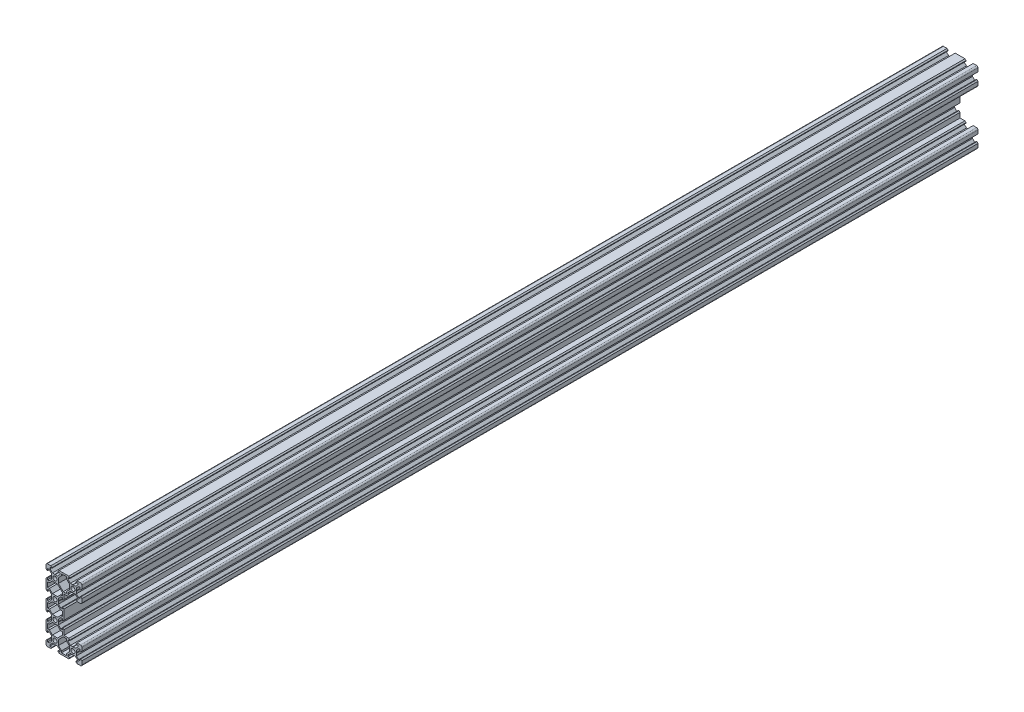
SolidWorks part; units mm, degrees
material "6061-T6 (SS)"
ref_plane "Front Plane" through (0, 0, 0) normal (0, 0, 1) x (1, 0, 0)
ref_plane "Top Plane" through (0, 0, 0) normal (0, 1, 0) x (1, 0, 0)
ref_plane "Right Plane" through (0, 0, 0) normal (1, 0, 0) x (0, 0, -1)
sketch "Sketch1" plane through (0, 0, 0) normal (0, 0, 1) x (1, 0, 0)
  line L0 (-20, -38.5) -> (-20, 38.5)
  line L1 (-18.5, 40) -> (18.5, 40)
  line L2 (20, 38.5) -> (20, 21.5)
  line L3 (18.5, 20) -> (0, 20)
  line L4 (0, 20) -> (0, -20)
  line L5 (0, 0) -> (-20, 0) construction
  line L6 (18.5, -20) -> (0, -20)
  line L7 (20, -38.5) -> (20, -21.5)
  line L8 (-18.5, -40) -> (18.5, -40)
  line L9 (20, 30) -> (10, 30) construction
  line L10 (-10, 0) -> (-10, 10) construction
  arc A0 (-18.5, -40) -> (-20, -38.5) centre (-18.5, -38.5) cw
  arc A1 (20, -38.5) -> (18.5, -40) centre (18.5, -38.5) cw
  arc A2 (18.5, -20) -> (20, -21.5) centre (18.5, -21.5) cw
  arc A3 (20, 21.5) -> (18.5, 20) centre (18.5, 21.5) cw
  arc A4 (18.5, 40) -> (20, 38.5) centre (18.5, 38.5) cw
  arc A5 (-20, 38.5) -> (-18.5, 40) centre (-18.5, 38.5) cw
  circle A6 centre (10, 30) radius 2.3
  circle A7 centre (-10, 30) radius 2.3
  circle A8 centre (-10, 10) radius 2.3
  circle A9 centre (-10, -10) radius 2.3
  circle A10 centre (10, -30) radius 2.3
  circle A11 centre (-10, -30) radius 2.3
  point P13 (-20, -40)
  point P16 (20, -40)
  point P19 (20, -20)
  point P22 (20, 20)
  point P25 (20, 40)
  point P28 (-20, 40)
  line B0 (-10, 30) -> (-10, 40) construction
  line B1 (-10, 33.69) -> (-10.21, 33.9)
  line B2 (-10.21, 33.9) -> (-12.8393, 33.9)
  line B3 (-12.8393, 33.9) -> (-15.5, 36.5607)
  line B4 (-15.5, 36.5607) -> (-15.5, 38.2)
  line B5 (-15.5, 38.2) -> (-13.395, 38.2)
  line B6 (-13.395, 38.2) -> (-13.395, 38.815)
  line B7 (-13.395, 38.815) -> (-14.58, 40)
  line B8 (-14.58, 40) -> (-5.42, 40)
  line B9 (-10, 30) -> (-15.9132, 35.9132) construction
  line B10 (-6.605, 38.815) -> (-5.42, 40)
  line B11 (-6.605, 38.2) -> (-6.605, 38.815)
  line B12 (-4.5, 38.2) -> (-6.605, 38.2)
  line B13 (-4.5, 36.5607) -> (-4.5, 38.2)
  line B14 (-7.1607, 33.9) -> (-4.5, 36.5607)
  line B15 (-9.79, 33.9) -> (-7.1607, 33.9)
  line B16 (-10, 33.69) -> (-9.79, 33.9)
  line B17 (10, 30) -> (10, 40) construction
  line B18 (10, 33.69) -> (9.79, 33.9)
  line B19 (9.79, 33.9) -> (7.1607, 33.9)
  line B20 (7.1607, 33.9) -> (4.5, 36.5607)
  line B21 (4.5, 36.5607) -> (4.5, 38.2)
  line B22 (4.5, 38.2) -> (6.605, 38.2)
  line B23 (6.605, 38.2) -> (6.605, 38.815)
  line B24 (6.605, 38.815) -> (5.42, 40)
  line B25 (5.42, 40) -> (14.58, 40)
  line B26 (10, 30) -> (4.0868, 35.9132) construction
  line B27 (13.395, 38.815) -> (14.58, 40)
  line B28 (13.395, 38.2) -> (13.395, 38.815)
  line B29 (15.5, 38.2) -> (13.395, 38.2)
  line B30 (15.5, 36.5607) -> (15.5, 38.2)
  line B31 (12.8393, 33.9) -> (15.5, 36.5607)
  line B32 (10.21, 33.9) -> (12.8393, 33.9)
  line B33 (10, 33.69) -> (10.21, 33.9)
  line B34 (10, -30) -> (10, -20) construction
  line B35 (10, -26.31) -> (9.79, -26.1)
  line B36 (9.79, -26.1) -> (7.1607, -26.1)
  line B37 (7.1607, -26.1) -> (4.5, -23.4393)
  line B38 (4.5, -23.4393) -> (4.5, -21.8)
  line B39 (4.5, -21.8) -> (6.605, -21.8)
  line B40 (6.605, -21.8) -> (6.605, -21.185)
  line B41 (6.605, -21.185) -> (5.42, -20)
  line B42 (5.42, -20) -> (14.58, -20)
  line B43 (10, -30) -> (4.0868, -24.0868) construction
  line B44 (13.395, -21.185) -> (14.58, -20)
  line B45 (13.395, -21.8) -> (13.395, -21.185)
  line B46 (15.5, -21.8) -> (13.395, -21.8)
  line B47 (15.5, -23.4393) -> (15.5, -21.8)
  line B48 (12.8393, -26.1) -> (15.5, -23.4393)
  line B49 (10.21, -26.1) -> (12.8393, -26.1)
  line B50 (10, -26.31) -> (10.21, -26.1)
  line B51 (-10, 30) -> (-20, 30) construction
  line B52 (-13.69, 30) -> (-13.9, 29.79)
  line B53 (-13.9, 29.79) -> (-13.9, 27.1607)
  line B54 (-13.9, 27.1607) -> (-16.5607, 24.5)
  line B55 (-16.5607, 24.5) -> (-18.2, 24.5)
  line B56 (-18.2, 24.5) -> (-18.2, 26.605)
  line B57 (-18.2, 26.605) -> (-18.815, 26.605)
  line B58 (-18.815, 26.605) -> (-20, 25.42)
  line B59 (-20, 25.42) -> (-20, 34.58)
  line B60 (-10, 30) -> (-15.9132, 24.0868) construction
  line B61 (-18.815, 33.395) -> (-20, 34.58)
  line B62 (-18.2, 33.395) -> (-18.815, 33.395)
  line B63 (-18.2, 35.5) -> (-18.2, 33.395)
  line B64 (-16.5607, 35.5) -> (-18.2, 35.5)
  line B65 (-13.9, 32.8393) -> (-16.5607, 35.5)
  line B66 (-13.9, 30.21) -> (-13.9, 32.8393)
  line B67 (-13.69, 30) -> (-13.9, 30.21)
  line B68 (-10, 10) -> (-20, 10) construction
  line B69 (-13.69, 10) -> (-13.9, 9.79)
  line B70 (-13.9, 9.79) -> (-13.9, 7.1607)
  line B71 (-13.9, 7.1607) -> (-16.5607, 4.5)
  line B72 (-16.5607, 4.5) -> (-18.2, 4.5)
  line B73 (-18.2, 4.5) -> (-18.2, 6.605)
  line B74 (-18.2, 6.605) -> (-18.815, 6.605)
  line B75 (-18.815, 6.605) -> (-20, 5.42)
  line B76 (-20, 5.42) -> (-20, 14.58)
  line B77 (-10, 10) -> (-15.9132, 4.0868) construction
  line B78 (-18.815, 13.395) -> (-20, 14.58)
  line B79 (-18.2, 13.395) -> (-18.815, 13.395)
  line B80 (-18.2, 15.5) -> (-18.2, 13.395)
  line B81 (-16.5607, 15.5) -> (-18.2, 15.5)
  line B82 (-13.9, 12.8393) -> (-16.5607, 15.5)
  line B83 (-13.9, 10.21) -> (-13.9, 12.8393)
  line B84 (-13.69, 10) -> (-13.9, 10.21)
  line B85 (-10, -10) -> (-20, -10) construction
  line B86 (-13.69, -10) -> (-13.9, -10.21)
  line B87 (-13.9, -10.21) -> (-13.9, -12.8393)
  line B88 (-13.9, -12.8393) -> (-16.5607, -15.5)
  line B89 (-16.5607, -15.5) -> (-18.2, -15.5)
  line B90 (-18.2, -15.5) -> (-18.2, -13.395)
  line B91 (-18.2, -13.395) -> (-18.815, -13.395)
  line B92 (-18.815, -13.395) -> (-20, -14.58)
  line B93 (-20, -14.58) -> (-20, -5.42)
  line B94 (-10, -10) -> (-15.9132, -15.9132) construction
  line B95 (-18.815, -6.605) -> (-20, -5.42)
  line B96 (-18.2, -6.605) -> (-18.815, -6.605)
  line B97 (-18.2, -4.5) -> (-18.2, -6.605)
  line B98 (-16.5607, -4.5) -> (-18.2, -4.5)
  line B99 (-13.9, -7.1607) -> (-16.5607, -4.5)
  line B100 (-13.9, -9.79) -> (-13.9, -7.1607)
  line B101 (-13.69, -10) -> (-13.9, -9.79)
  line B102 (-10, -30) -> (-20, -30) construction
  line B103 (-13.69, -30) -> (-13.9, -30.21)
  line B104 (-13.9, -30.21) -> (-13.9, -32.8393)
  line B105 (-13.9, -32.8393) -> (-16.5607, -35.5)
  line B106 (-16.5607, -35.5) -> (-18.2, -35.5)
  line B107 (-18.2, -35.5) -> (-18.2, -33.395)
  line B108 (-18.2, -33.395) -> (-18.815, -33.395)
  line B109 (-18.815, -33.395) -> (-20, -34.58)
  line B110 (-20, -34.58) -> (-20, -25.42)
  line B111 (-10, -30) -> (-15.9132, -35.9132) construction
  line B112 (-18.815, -26.605) -> (-20, -25.42)
  line B113 (-18.2, -26.605) -> (-18.815, -26.605)
  line B114 (-18.2, -24.5) -> (-18.2, -26.605)
  line B115 (-16.5607, -24.5) -> (-18.2, -24.5)
  line B116 (-13.9, -27.1607) -> (-16.5607, -24.5)
  line B117 (-13.9, -29.79) -> (-13.9, -27.1607)
  line B118 (-13.69, -30) -> (-13.9, -29.79)
  line B119 (-10, -30) -> (-10, -40) construction
  line B120 (-10, -33.69) -> (-9.79, -33.9)
  line B121 (-9.79, -33.9) -> (-7.1607, -33.9)
  line B122 (-7.1607, -33.9) -> (-4.5, -36.5607)
  line B123 (-4.5, -36.5607) -> (-4.5, -38.2)
  line B124 (-4.5, -38.2) -> (-6.605, -38.2)
  line B125 (-6.605, -38.2) -> (-6.605, -38.815)
  line B126 (-6.605, -38.815) -> (-5.42, -40)
  line B127 (-5.42, -40) -> (-14.58, -40)
  line B128 (-10, -30) -> (-4.0868, -35.9132) construction
  line B129 (-13.395, -38.815) -> (-14.58, -40)
  line B130 (-13.395, -38.2) -> (-13.395, -38.815)
  line B131 (-15.5, -38.2) -> (-13.395, -38.2)
  line B132 (-15.5, -36.5607) -> (-15.5, -38.2)
  line B133 (-12.8393, -33.9) -> (-15.5, -36.5607)
  line B134 (-10.21, -33.9) -> (-12.8393, -33.9)
  line B135 (-10, -33.69) -> (-10.21, -33.9)
  line B136 (10, -30) -> (10, -40) construction
  line B137 (10, -33.69) -> (10.21, -33.9)
  line B138 (10.21, -33.9) -> (12.8393, -33.9)
  line B139 (12.8393, -33.9) -> (15.5, -36.5607)
  line B140 (15.5, -36.5607) -> (15.5, -38.2)
  line B141 (15.5, -38.2) -> (13.395, -38.2)
  line B142 (13.395, -38.2) -> (13.395, -38.815)
  line B143 (13.395, -38.815) -> (14.58, -40)
  line B144 (14.58, -40) -> (5.42, -40)
  line B145 (10, -30) -> (15.9132, -35.9132) construction
  line B146 (6.605, -38.815) -> (5.42, -40)
  line B147 (6.605, -38.2) -> (6.605, -38.815)
  line B148 (4.5, -38.2) -> (6.605, -38.2)
  line B149 (4.5, -36.5607) -> (4.5, -38.2)
  line B150 (7.1607, -33.9) -> (4.5, -36.5607)
  line B151 (9.79, -33.9) -> (7.1607, -33.9)
  line B152 (10, -33.69) -> (9.79, -33.9)
  line B153 (10, 30) -> (10, 20) construction
  line B154 (10, 26.31) -> (10.21, 26.1)
  line B155 (10.21, 26.1) -> (12.8393, 26.1)
  line B156 (12.8393, 26.1) -> (15.5, 23.4393)
  line B157 (15.5, 23.4393) -> (15.5, 21.8)
  line B158 (15.5, 21.8) -> (13.395, 21.8)
  line B159 (13.395, 21.8) -> (13.395, 21.185)
  line B160 (13.395, 21.185) -> (14.58, 20)
  line B161 (14.58, 20) -> (5.42, 20)
  line B162 (10, 30) -> (15.9132, 24.0868) construction
  line B163 (6.605, 21.185) -> (5.42, 20)
  line B164 (6.605, 21.8) -> (6.605, 21.185)
  line B165 (4.5, 21.8) -> (6.605, 21.8)
  line B166 (4.5, 23.4393) -> (4.5, 21.8)
  line B167 (7.1607, 26.1) -> (4.5, 23.4393)
  line B168 (9.79, 26.1) -> (7.1607, 26.1)
  line B169 (10, 26.31) -> (9.79, 26.1)
  line B170 (-10, 10) -> (0, 10) construction
  line B171 (-6.31, 10) -> (-6.1, 10.21)
  line B172 (-6.1, 10.21) -> (-6.1, 12.8393)
  line B173 (-6.1, 12.8393) -> (-3.4393, 15.5)
  line B174 (-3.4393, 15.5) -> (-1.8, 15.5)
  line B175 (-1.8, 15.5) -> (-1.8, 13.395)
  line B176 (-1.8, 13.395) -> (-1.185, 13.395)
  line B177 (-1.185, 13.395) -> (0, 14.58)
  line B178 (0, 14.58) -> (0, 5.42)
  line B179 (-10, 10) -> (-4.0868, 15.9132) construction
  line B180 (-1.185, 6.605) -> (0, 5.42)
  line B181 (-1.8, 6.605) -> (-1.185, 6.605)
  line B182 (-1.8, 4.5) -> (-1.8, 6.605)
  line B183 (-3.4393, 4.5) -> (-1.8, 4.5)
  line B184 (-6.1, 7.1607) -> (-3.4393, 4.5)
  line B185 (-6.1, 9.79) -> (-6.1, 7.1607)
  line B186 (-6.31, 10) -> (-6.1, 9.79)
  line B187 (-10, -10) -> (0, -10) construction
  line B188 (-6.31, -10) -> (-6.1, -9.79)
  line B189 (-6.1, -9.79) -> (-6.1, -7.1607)
  line B190 (-6.1, -7.1607) -> (-3.4393, -4.5)
  line B191 (-3.4393, -4.5) -> (-1.8, -4.5)
  line B192 (-1.8, -4.5) -> (-1.8, -6.605)
  line B193 (-1.8, -6.605) -> (-1.185, -6.605)
  line B194 (-1.185, -6.605) -> (0, -5.42)
  line B195 (0, -5.42) -> (0, -14.58)
  line B196 (-10, -10) -> (-4.0868, -4.0868) construction
  line B197 (-1.185, -13.395) -> (0, -14.58)
  line B198 (-1.8, -13.395) -> (-1.185, -13.395)
  line B199 (-1.8, -15.5) -> (-1.8, -13.395)
  line B200 (-3.4393, -15.5) -> (-1.8, -15.5)
  line B201 (-6.1, -12.8393) -> (-3.4393, -15.5)
  line B202 (-6.1, -10.21) -> (-6.1, -12.8393)
  line B203 (-6.31, -10) -> (-6.1, -10.21)
  line B204 (10, -30) -> (20, -30) construction
  line B205 (13.69, -30) -> (13.9, -29.79)
  line B206 (13.9, -29.79) -> (13.9, -27.1607)
  line B207 (13.9, -27.1607) -> (16.5607, -24.5)
  line B208 (16.5607, -24.5) -> (18.2, -24.5)
  line B209 (18.2, -24.5) -> (18.2, -26.605)
  line B210 (18.2, -26.605) -> (18.815, -26.605)
  line B211 (18.815, -26.605) -> (20, -25.42)
  line B212 (20, -25.42) -> (20, -34.58)
  line B213 (10, -30) -> (15.9132, -24.0868) construction
  line B214 (18.815, -33.395) -> (20, -34.58)
  line B215 (18.2, -33.395) -> (18.815, -33.395)
  line B216 (18.2, -35.5) -> (18.2, -33.395)
  line B217 (16.5607, -35.5) -> (18.2, -35.5)
  line B218 (13.9, -32.8393) -> (16.5607, -35.5)
  line B219 (13.9, -30.21) -> (13.9, -32.8393)
  line B220 (13.69, -30) -> (13.9, -30.21)
  line B221 (10, 30) -> (20, 30) construction
  line B222 (13.69, 30) -> (13.9, 30.21)
  line B223 (13.9, 30.21) -> (13.9, 32.8393)
  line B224 (13.9, 32.8393) -> (16.5607, 35.5)
  line B225 (16.5607, 35.5) -> (18.2, 35.5)
  line B226 (18.2, 35.5) -> (18.2, 33.395)
  line B227 (18.2, 33.395) -> (18.815, 33.395)
  line B228 (18.815, 33.395) -> (20, 34.58)
  line B229 (20, 34.58) -> (20, 25.42)
  line B230 (10, 30) -> (15.9132, 35.9132) construction
  line B231 (18.815, 26.605) -> (20, 25.42)
  line B232 (18.2, 26.605) -> (18.815, 26.605)
  line B233 (18.2, 24.5) -> (18.2, 26.605)
  line B234 (16.5607, 24.5) -> (18.2, 24.5)
  line B235 (13.9, 27.1607) -> (16.5607, 24.5)
  line B236 (13.9, 29.79) -> (13.9, 27.1607)
  line B237 (13.69, 30) -> (13.9, 29.79)
  line B238 (-18.2, -2.7) -> (-18.2, 2.7)
  line B239 (-18.2, 2.7) -> (-16.2393, 2.7)
  line B240 (-16.2393, 2.7) -> (-12.8393, 6.1)
  line B241 (-12.8393, 6.1) -> (-7.1607, 6.1)
  line B242 (-10, 6.1) -> (-10, 0) construction
  line B243 (-10, 0) -> (-18.2, 0) construction
  line B244 (-3.7607, 2.7) -> (-7.1607, 6.1)
  line B245 (-1.8, 2.7) -> (-3.7607, 2.7)
  line B246 (-1.8, -2.7) -> (-1.8, 2.7)
  line B247 (-1.8, -2.7) -> (-3.7607, -2.7)
  line B248 (-3.7607, -2.7) -> (-7.1607, -6.1)
  line B249 (-12.8393, -6.1) -> (-7.1607, -6.1)
  line B250 (-16.2393, -2.7) -> (-12.8393, -6.1)
  line B251 (-18.2, -2.7) -> (-16.2393, -2.7)
  line B252 (-10, 6.1) -> (-10, 10) construction
  line B253 (-10, 10) -> (-15.0927, 4.9073) construction
  line B254 (-18.2, 17.3) -> (-18.2, 22.7)
  line B255 (-18.2, 22.7) -> (-16.2393, 22.7)
  line B256 (-16.2393, 22.7) -> (-12.8393, 26.1)
  line B257 (-12.8393, 26.1) -> (-7.1607, 26.1)
  line B258 (-10, 26.1) -> (-10, 20) construction
  line B259 (-10, 20) -> (-18.2, 20) construction
  line B260 (-1.8, 17.3) -> (-3.7607, 17.3)
  line B261 (-3.7607, 17.3) -> (-7.1607, 13.9)
  line B262 (-12.8393, 13.9) -> (-7.1607, 13.9)
  line B263 (-16.2393, 17.3) -> (-12.8393, 13.9)
  line B264 (-18.2, 17.3) -> (-16.2393, 17.3)
  line B265 (-10, 26.1) -> (-10, 30) construction
  line B266 (-10, 30) -> (-15.0927, 24.9073) construction
  line B267 (-7.1607, 26.1) -> (-1.8, 20.7393)
  line B268 (-1.8, 17.3) -> (-1.8, 20.7393)
  line B269 (2.7, -38.2) -> (-2.7, -38.2)
  line B270 (-2.7, -38.2) -> (-2.7, -36.2393)
  line B271 (-2.7, -36.2393) -> (-6.1, -32.8393)
  line B272 (-6.1, -32.8393) -> (-6.1, -27.1607)
  line B273 (-6.1, -30) -> (0, -30) construction
  line B274 (0, -30) -> (0, -38.2) construction
  line B275 (2.7, -21.8) -> (2.7, -23.7607)
  line B276 (2.7, -23.7607) -> (6.1, -27.1607)
  line B277 (6.1, -32.8393) -> (6.1, -27.1607)
  line B278 (2.7, -36.2393) -> (6.1, -32.8393)
  line B279 (2.7, -38.2) -> (2.7, -36.2393)
  line B280 (-6.1, -30) -> (-10, -30) construction
  line B281 (-10, -30) -> (-4.9073, -35.0927) construction
  line B282 (-6.1, -27.1607) -> (-0.7393, -21.8)
  line B283 (2.7, -21.8) -> (-0.7393, -21.8)
  line B284 (-18.2, -22.7) -> (-18.2, -17.3)
  line B285 (-18.2, -17.3) -> (-16.2393, -17.3)
  line B286 (-16.2393, -17.3) -> (-12.8393, -13.9)
  line B287 (-12.8393, -13.9) -> (-7.1607, -13.9)
  line B288 (-10, -13.9) -> (-10, -20) construction
  line B289 (-10, -20) -> (-18.2, -20) construction
  line B290 (-12.8393, -26.1) -> (-7.1607, -26.1)
  line B291 (-16.2393, -22.7) -> (-12.8393, -26.1)
  line B292 (-18.2, -22.7) -> (-16.2393, -22.7)
  line B293 (-10, -13.9) -> (-10, -10) construction
  line B294 (-10, -10) -> (-15.0927, -15.0927) construction
  line B295 (-3.7607, -17.3) -> (-7.1607, -13.9)
  line B296 (-1.8, -17.3) -> (-3.7607, -17.3)
  line B297 (-1.8, -17.3) -> (-1.8, -20.7393)
  line B298 (-1.8, -20.7393) -> (-7.1607, -26.1)
  line B299 (-2.7, 38.2) -> (2.7, 38.2)
  line B300 (2.7, 38.2) -> (2.7, 36.2393)
  line B301 (2.7, 36.2393) -> (6.1, 32.8393)
  line B302 (6.1, 32.8393) -> (6.1, 27.1607)
  line B303 (6.1, 30) -> (0, 30) construction
  line B304 (0, 30) -> (0, 38.2) construction
  line B305 (-6.1, 32.8393) -> (-6.1, 27.1607)
  line B306 (-2.7, 36.2393) -> (-6.1, 32.8393)
  line B307 (-2.7, 38.2) -> (-2.7, 36.2393)
  line B308 (6.1, 30) -> (10, 30) construction
  line B309 (10, 30) -> (4.9073, 35.0927) construction
  line B310 (2.7, 23.7607) -> (6.1, 27.1607)
  line B311 (2.7, 21.8) -> (2.7, 23.7607)
  line B312 (2.7, 21.8) -> (-0.7393, 21.8)
  line B313 (-0.7393, 21.8) -> (-6.1, 27.1607)
  dimension "D3" = 1.5
  dimension "D6" = 4.6
  dimension "D7" = 20
  dimension "D8" = 20
  dimension "D1" = 40
  dimension "D2" = 80
  dimension "D4" = 20
  dimension "D5" = 20
sketch_block_instance "V Slot 2-1"
sketch_block "V Slot 2" parameters "D1"=10, "D2"=11, "D3"=4.3, "D4"=1.8, "D5"=0.21, "D6"=45, "D7"=9.16, "D8"=1.5, "D9"=6.79
sketch_block_instance "V Slot 2-2"
sketch_block_instance "V Slot 2-3"
sketch_block_instance "V Slot 2-4"
sketch_block_instance "V Slot 2-5"
sketch_block_instance "V Slot 2-6"
sketch_block_instance "V Slot 2-7"
sketch_block_instance "V Slot 2-8"
sketch_block_instance "V Slot 2-9"
sketch_block_instance "V Slot 2-10"
sketch_block_instance "V Slot 2-11"
sketch_block_instance "V Slot 2-12"
sketch_block_instance "V Slot 2-13"
sketch_block_instance "V Slot 2-14"
sketch_block_instance "Center Cutout 1-1"
sketch_block "Center Cutout 1" parameters "D1"=5.4, "D2"=12.2, "D3"=8.2, "D4"=45, "D5"=10, "D6"=1.5
sketch_block_instance "Corner Cutout 1-1"
sketch_block "Corner Cutout 1" parameters "D1"=5.4, "D2"=12.2, "D3"=8.2, "D4"=45, "D5"=10, "D6"=1.5
sketch_block_instance "Corner Cutout 1-2"
sketch_block_instance "Corner Cutout 2-1"
sketch_block "Corner Cutout 2" parameters "D1"=5.4, "D2"=12.2, "D3"=8.2, "D4"=45, "D5"=10, "D6"=1.5
sketch_block_instance "Corner Cutout 2-2"
extrude "Boss-Extrude1" add sketch "Sketch1" along normal blind 1000 contours B237 B222 B223 B224 B225 B226 B227 B228 L2 A4 L1 B27 B28 B29 B30 B31 B32 B33 B18 B19 B20 B21 B22 B23 B24 B10 B11 B12 B13 B14 B15 B16 B1 B2 B3 B4 B5 B6 B7 A5 L0 B61 B62 B63 B64 B65 B66 B67 B52
